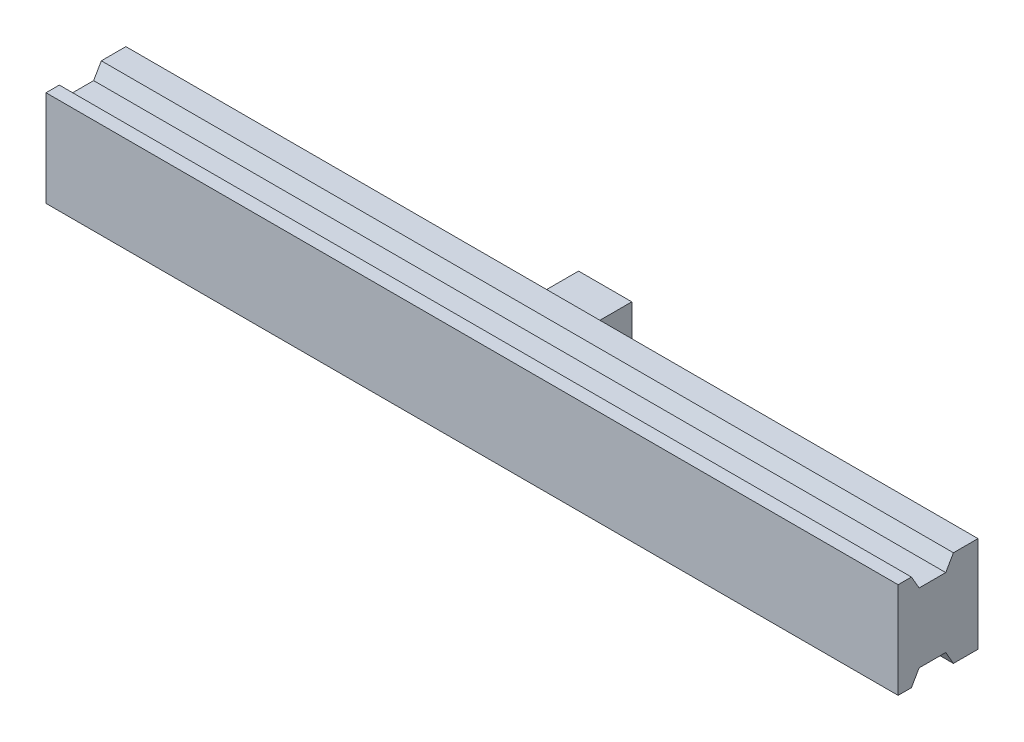
SolidWorks part; units mm, degrees
ref_plane "Front Plane" through (0, 0, 0) normal (0, 0, 1) x (1, 0, 0)
ref_plane "Top Plane" through (0, 0, 0) normal (0, 1, 0) x (1, 0, 0)
ref_plane "Right Plane" through (0, 0, 0) normal (1, 0, 0) x (0, 0, -1)
sketch "Sketch1" plane through (0, 0, 0) normal (0, 0, 1) x (1, 0, 0)
  line L1 (335.087, 98.3824) -> (495.087, 98.3824)
  line L2 (335.087, 98.3824) -> (335.087, 80.3824)
  line L3 (335.087, 80.3824) -> (495.087, 80.3824)
  line L4 (495.087, 98.3824) -> (495.087, 80.3824)
  line L5 (335.087, 98.3824) -> (495.087, 80.3824) construction
  line L6 (335.087, 80.3824) -> (495.087, 98.3824) construction
  point P0 (415.087, 89.3824)
  dimension "D1" = 160
  dimension "D2" = 18
extrude "Boss-Extrude1" add sketch "Sketch1" along normal blind 15
sketch "Sketch2" plane through (495.087, 0, 0) normal (1, 0, 0) x (0, 0, -1)
  line L0 (-12.5, 98.3824) -> (-11.0566, 95.8824)
  line L1 (-15, 98.3824) -> (0, 98.3824) construction
  line L2 (-11.0566, 95.8824) -> (-6.0566, 95.8824)
  line L3 (-6.0566, 95.8824) -> (-4.6132, 98.3824)
  line L4 (-4.6132, 98.3824) -> (-12.5, 98.3824)
  line L5 (-15, 89.3824) -> (903.7795, 89.3824) construction
  line L6 (-15, 80.3824) -> (-15, 98.3824) construction
  line L7 (903.7795, -398.3345) -> (903.7795, -213.3345) construction
  line L8 (-12.5, 98.3824) -> (-12.5, 95.8824) construction
  line L9 (-12.5, 80.3824) -> (-12.5, 82.8824) construction
  line L10 (-4.6132, 80.3824) -> (-12.5, 80.3824)
  line L11 (-6.0566, 82.8824) -> (-4.6132, 80.3824)
  line L12 (-11.0566, 82.8824) -> (-6.0566, 82.8824)
  line L13 (-12.5, 80.3824) -> (-11.0566, 82.8824)
  dimension "D1" = 60
  dimension "D2" = 2.5
  dimension "D3" = 5
  dimension "D4" = 2.5
  dimension "D5" = 60
extrude "Cut-Extrude1" cut sketch "Sketch2" against normal through all
sketch "Sketch3" plane through (0, 0, 0) normal (0, 0, -1) x (-1, 0, 0)
  line L0 (-495.087, 89.3824) -> (-335.087, 89.3824) construction
  line L1 (-495.087, 80.3824) -> (-495.087, 98.3824) construction
  line L2 (-335.087, 98.3824) -> (-335.087, 80.3824) construction
  line L3 (-415.087, 98.3824) -> (-415.087, 80.3824) construction
  line L4 (-495.087, 98.3824) -> (-335.087, 98.3824) construction
  line L5 (-335.087, 80.3824) -> (-495.087, 80.3824) construction
  line L7 (-420.087, 94.3824) -> (-410.087, 94.3824)
  line L8 (-420.087, 94.3824) -> (-420.087, 84.3824)
  line L9 (-420.087, 84.3824) -> (-410.087, 84.3824)
  line L10 (-410.087, 94.3824) -> (-410.087, 84.3824)
  line L11 (-420.087, 94.3824) -> (-410.087, 84.3824) construction
  line L12 (-420.087, 84.3824) -> (-410.087, 94.3824) construction
  point P12 (-415.087, 89.3824)
  dimension "D1" = 10
  dimension "D2" = 10
extrude "Boss-Extrude2" add sketch "Sketch3" along normal blind 10
